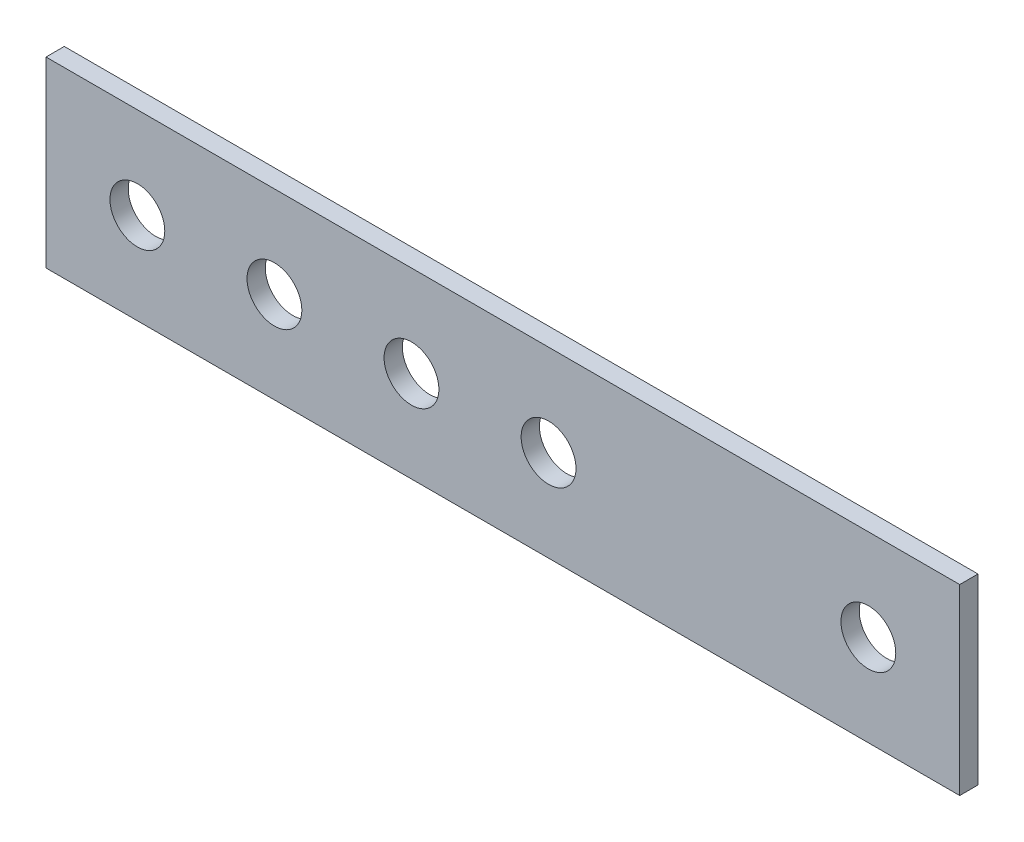
SolidWorks part; units mm, degrees
material "Copper"
ref_plane "Front Plane" through (0, 0, 0) normal (0, 0, 1) x (1, 0, 0)
ref_plane "Top Plane" through (0, 0, 0) normal (0, 1, 0) x (1, 0, 0)
ref_plane "Right Plane" through (0, 0, 0) normal (1, 0, 0) x (0, 0, -1)
sketch "Sketch1" plane through (0, 0, 0) normal (0, 0, 1) x (1, 0, 0)
  line L0 (-100, 0) -> (100, 0) construction
  line L1 (-100, 20) -> (100, 20)
  line L2 (-100, 20) -> (-100, -20)
  line L3 (-100, -20) -> (100, -20)
  line L4 (100, 20) -> (100, -20)
  line L5 (-100, 20) -> (100, -20) construction
  line L6 (-100, -20) -> (100, 20) construction
  circle A0 centre (80, 0) radius 6
  point P0 (0, 0)
  dimension "D3" = 12
  dimension "D4" = 20
  dimension "D1" = 40
  dimension "D2" = 200
extrude "Boss-Extrude1" add sketch "Sketch1" along normal mid plane 4
sketch "Sketch2" plane through (0, 0, 2) normal (0, 0, 1) x (1, 0, 0)
  line L0 (-100, 0) -> (100, 0) construction
  line L1 (-100, 20) -> (-100, -20) construction
  circle A0 centre (-80, 0) radius 6
  dimension "D1" = 12
  dimension "D2" = 20
extrude "Cut-Extrude1" cut sketch "Sketch2" against normal through all
pattern_linear "LPattern1" count 4 spacing 30 along (1, 0, 0) of "Cut-Extrude1"
